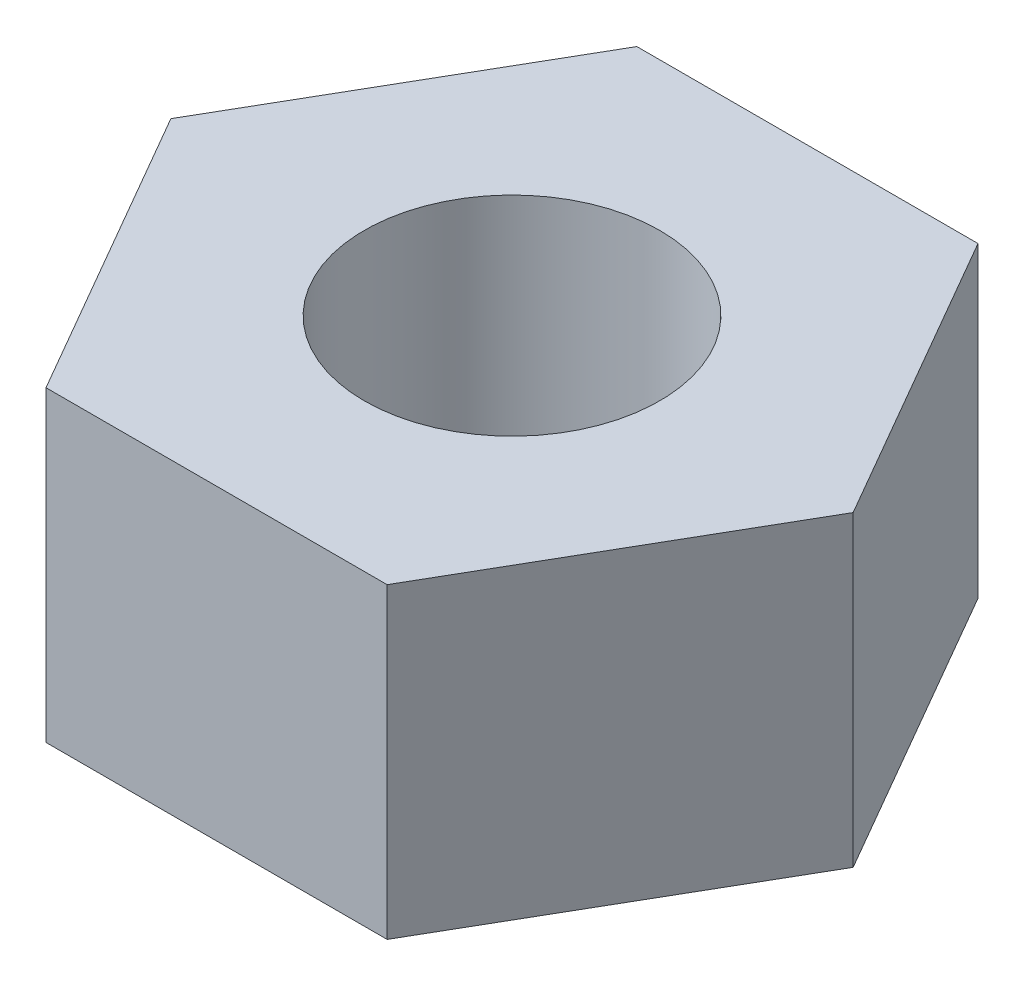
SolidWorks part; units mm, degrees
ref_plane "Plan de face" through (0, 0, 0) normal (0, 0, 1) x (1, 0, 0)
ref_plane "Plan de dessus" through (0, 0, 0) normal (0, 1, 0) x (1, 0, 0)
ref_plane "Plan de droite" through (0, 0, 0) normal (1, 0, 0) x (0, 0, -1)
sketch "Esquisse1" plane through (0, 0, 0) normal (0, 1, 0) x (1, 0, 0)
  line L12 (-2.8868, 5) -> (-5.7735, 0)
  line L13 (-2.8868, 5) -> (2.8868, 5)
  line L14 (-2.8868, 5) -> (-2.8868, -5) construction
  line L15 (-2.8868, -5) -> (2.8868, -5)
  line L16 (2.8868, 5) -> (2.8868, -5) construction
  line L17 (-5.7735, 0) -> (-2.8868, -5)
  line L18 (2.8868, 5) -> (5.7735, 0)
  line L19 (5.7735, 0) -> (2.8868, -5)
  line L20 (-2.8868, 5) -> (2.8868, -5) construction
  circle A0 centre (0, 0) radius 2.5
  dimension "D3" = 5
  dimension "D1" = 120
  dimension "D2" = 10
extrude "Boss.-Extru.1" add sketch "Esquisse1" along normal blind 5.2
